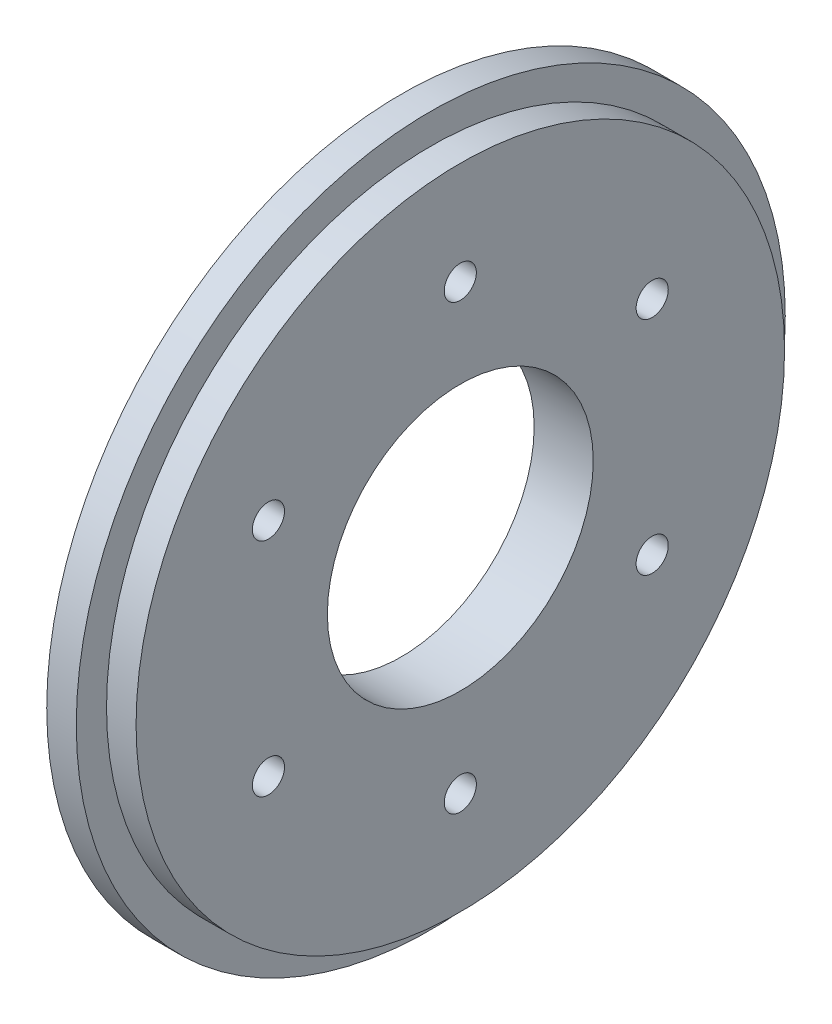
SolidWorks part; units mm, degrees
ref_plane "Front Plane" through (0, 0, 0) normal (0, 0, 1) x (1, 0, 0)
ref_plane "Top Plane" through (0, 0, 0) normal (0, 1, 0) x (1, 0, 0)
ref_plane "Right Plane" through (0, 0, 0) normal (1, 0, 0) x (0, 0, -1)
sketch "Sketch1" plane through (0, 0, 0) normal (1, 0, 0) x (0, 0, -1)
  circle A0 centre (0, 0) radius 38.1
  dimension "D1" = 76.2
extrude "Boss-Extrude1" add sketch "Sketch1" along normal blind 6.35
sketch "Sketch3" plane through (6.35, 0, 0) normal (1, 0, 0) x (0, 0, -1)
  circle A0 centre (0, 0) radius 38.1 construction
  circle A1 centre (0, 0) radius 38.1
extrude "Cut-Extrude-Thin1" cut sketch "Sketch3" against normal blind 3.175 thin thin type one direction reverse wall 3.2512
hole_wizard "1/2 (0.5) Diameter Hole1" positions "Sketch4" profile "Sketch5" hole size "1/2" standard "ANSI Inch" end condition through all
sketch "Sketch4" plane through (6.35, 0, 0) normal (1, 0, 0) x (0, 0, -1)
  point P0 (0, 0)
sketch "Sketch5" plane through (6.35, 0, 0) normal (0, 1, 0) x (0, 0, -1)
  line L0 (0, 0) -> (0, 6.35)
  line L1 (0, 6.35) -> (14.2875, 6.35)
  line L2 (14.2875, 6.35) -> (14.2875, 0)
  line L5 (14.2875, 0) -> (0, 0)
  line L11 (0, -6.35) -> (0, 107.95) construction
  dimension "Thru Hole Dia." = 28.575
  dimension "Thru Hole Depth" = 6.35
hole_wizard "#8-32 Tapped Hole1" positions "Sketch6" profile "Sketch7" tap size "#8-32" standard "ANSI Inch" end condition through all
sketch "Sketch6" plane through (0, 0, 0) normal (-1, 0, 0) x (0, 0, 1)
  point P0 (0, 23.8125)
  dimension "D1" = 23.8125
sketch "Sketch7" plane through (0, 23.8125, 0) normal (0, 1, 0) x (0, 0, 1)
  line L0 (0, 0) -> (0, 6.35)
  line L1 (0, 6.35) -> (1.7272, 6.35)
  line L2 (1.7272, 6.35) -> (1.7272, 0)
  line L5 (1.7272, 0) -> (0, 0)
  line L11 (0, -6.35) -> (0, 107.95) construction
  dimension "Thru Tap Drill Dia." = 3.4544
  dimension "Thru Tap Drill Depth" = 6.35
cosmetic thread "Hole Thread1" parameters "D2"=4.1656
pattern_circular "CirPattern1" count 6 over 360 about axis through (0, 0, 0) along (1, 0, 0) of "#8-32 Tapped Hole1"
